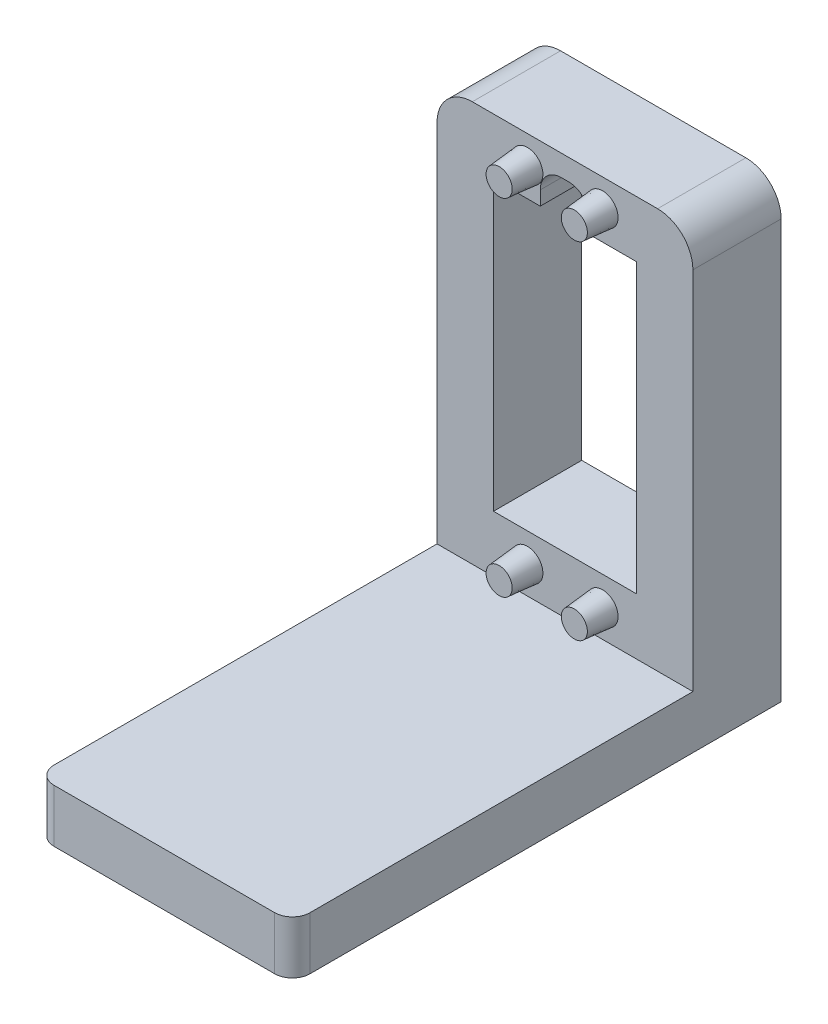
SolidWorks part; units mm, degrees
ref_plane "Front Plane" through (0, 0, 0) normal (0, 0, 1) x (1, 0, 0)
ref_plane "Top Plane" through (0, 0, 0) normal (0, 1, 0) x (1, 0, 0)
ref_plane "Right Plane" through (0, 0, 0) normal (1, 0, 0) x (0, 0, -1)
sketch "Sketch1" plane through (0, 0, 0) normal (0, 0, 1) x (1, 0, 0)
  line L0 (-8, 48.75) -> (28.25, 48.75)
  line L5 (0, 0) -> (20.25, 0)
  line L6 (0, 0) -> (0, 40.75)
  line L7 (0, 40.75) -> (20.25, 40.75)
  line L8 (20.25, 0) -> (20.25, 40.75)
  line L9 (28.25, -8) -> (28.25, 48.75)
  line L10 (-8, -8) -> (28.25, -8)
  line L11 (-8, -8) -> (-8, 48.75)
  dimension "D1" = 20.25
  dimension "D2" = 40.75
  dimension "D3" = 8
extrude "Boss-Extrude1" add sketch "Sketch1" along normal blind 12.5
sketch "Sketch3" plane through (0, 0, 12.5) normal (0, 0, 1) x (1, 0, 0)
  line L0 (-8, -8) -> (28.25, -8)
  line L1 (-8, -8) -> (-8, -15.5)
  line L2 (28.25, -8) -> (28.25, -15.5)
  line L3 (-8, -15.5) -> (28.25, -15.5)
  dimension "D1" = 7.5
extrude "Boss-Extrude2" add sketch "Sketch3" along normal blind 56.75 and the other way up to surface (12.5 mm away) other way up to face at (10.125, 20.375, 0)
sketch "Sketch4" plane through (0, 0, 12.5) normal (0, 0, 1) x (1, 0, 0)
  line L0 (20.25, 40.75) -> (0, 40.75) construction
  line L1 (6.625, 40.75) -> (13.625, 40.75)
  line L2 (6.625, 40.75) -> (6.625, 42.75)
  line L3 (9.625, 45.75) -> (10.625, 45.75)
  line L4 (13.625, 40.75) -> (13.625, 42.75)
  arc A0 (9.625, 45.75) -> (6.625, 42.75) centre (9.625, 42.75) ccw
  arc A1 (10.625, 45.75) -> (13.625, 42.75) centre (10.625, 42.75) cw
  point P6 (10.125, 40.75)
  point P7 (10.125, 40.75)
  point P10 (6.625, 45.75)
  point P13 (13.625, 45.75)
  dimension "D3" = 3
  dimension "D1" = 7
  dimension "D2" = 5
extrude "Cut-Extrude1" cut sketch "Sketch4" against normal through all
sketch "Sketch5" plane through (0, 0, 12.5) normal (0, 0, 1) x (1, 0, 0)
  line L0 (0, 40.75) -> (0, 48.75) construction
  line L1 (28.25, 48.75) -> (-8, 48.75) construction
  line L2 (0, 47.05) -> (7, 47.05) construction
  line L3 (7, 47.05) -> (7, 48.75) construction
  line L4 (6.625, 40.75) -> (0, 40.75) construction
  line L5 (7, 47.05) -> (7, 40.75) construction
  line L6 (10.125, 45.75) -> (10.125, 48.75) construction
  line L7 (10.625, 45.75) -> (9.625, 45.75) construction
  line L8 (0, 20.375) -> (20.25, 20.375) construction
  line L9 (0, 40.75) -> (0, 0) construction
  line L10 (20.25, 0) -> (20.25, 40.75) construction
  circle A0 centre (4.8, 44.85) radius 2.2
  circle A1 centre (15.45, 44.85) radius 2.2
  circle A2 centre (15.45, -4.1) radius 2.2
  circle A3 centre (4.8, -4.1) radius 2.2
  dimension "D3" = 4.4
  dimension "D1" = 7
  dimension "D2" = 6.3
extrude "Boss-Extrude3" add sketch "Sketch5" along normal blind 4 draft 5
fillet "Fillet1" radius 5 2 edges at (28.25, 48.75, 6.25) (-8, 48.75, 6.25)
fillet "Fillet2" radius 2.5 2 edges at (-8, -11.75, 69.25) (28.25, -11.75, 69.25)
